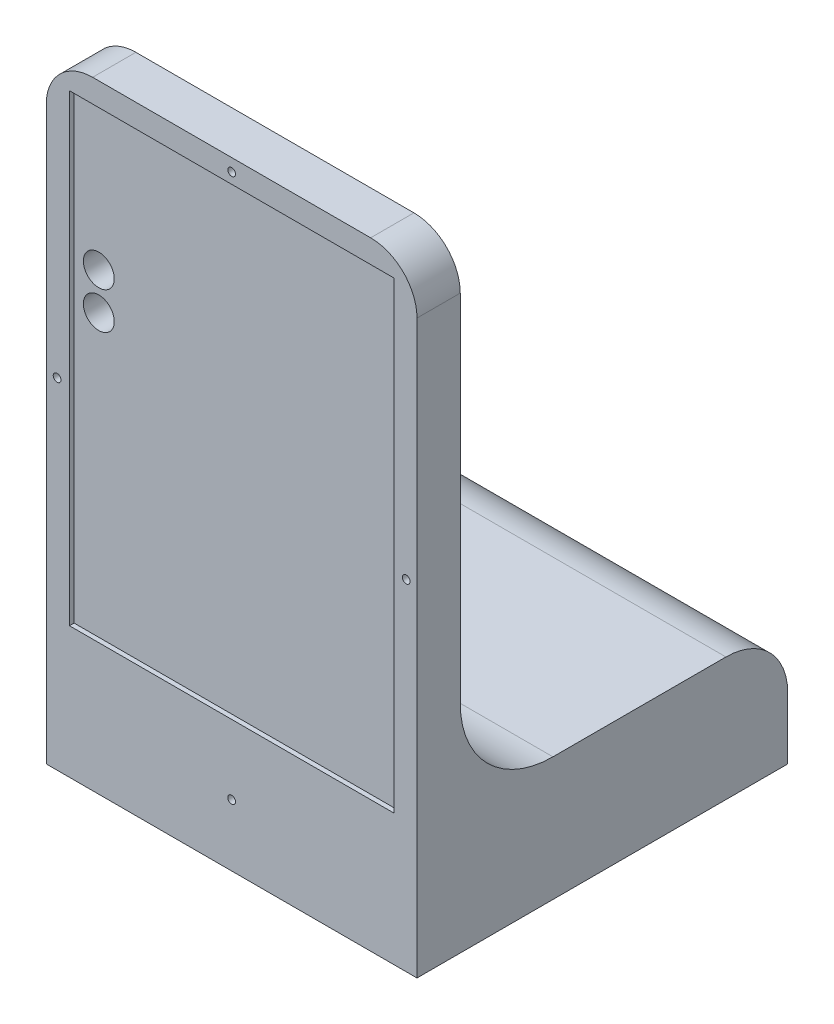
SolidWorks part; units mm, degrees
material "CA"
ref_plane "Plan de face" through (0, 0, 0) normal (0, 0, 1) x (1, 0, 0)
ref_plane "Plan de dessus" through (0, 0, 0) normal (0, 1, 0) x (1, 0, 0)
ref_plane "Plan de droite" through (0, 0, 0) normal (1, 0, 0) x (0, 0, -1)
sketch "Esquisse1" plane through (0, 0, 0) normal (0, 0, 1) x (1, 0, 0)
  line L0 (0, 40) -> (120, 40)
  line L1 (0, 0) -> (120, 0)
  line L2 (0, 0) -> (0, 200)
  line L3 (0, 200) -> (120, 200)
  line L4 (120, 0) -> (120, 200)
  dimension "D1" = 200
  dimension "D2" = 120
  dimension "D3" = 40
extrude "Boss.-Extru.2" add sketch "Esquisse1" along normal mid plane 50 contours L2 L1 L4 L3
sketch "Esquisse3" plane through (0, 0, 25) normal (0, 0, 1) x (1, 0, 0)
  line L0 (120, 0) -> (120, 200) construction
  line L1 (0, 0) -> (120, 0)
  line L2 (0, 0) -> (0, 40)
  line L3 (0, 40) -> (120, 40)
  line L4 (120, 0) -> (120, 40)
  dimension "D1" = 40
extrude "Boss.-Extru.3" add sketch "Esquisse3" along normal blind 70
fillet "Congé1" radius 15 1 edges at (60, 40, 25)
sketch "Esquisse4" plane through (0, 0, -25) normal (0, 0, -1) x (-1, 0, 0)
  line L0 (-120, 0) -> (-120, 200) construction
  line L1 (0, 0) -> (-120, 0)
  line L2 (0, 0) -> (0, 40)
  line L3 (0, 40) -> (-120, 40)
  line L4 (-120, 0) -> (-120, 40)
  dimension "D1" = 40
extrude "Boss.-Extru.4" add sketch "Esquisse4" along normal blind 140
fillet "Congé2" radius 30 1 edges at (60, 40, -25)
sketch "Esquisse5" plane through (0, 0, 95) normal (0, 0, 1) x (1, 0, 0)
  line L0 (0, 0) -> (120, 0) construction
  line L2 (120, 0) -> (120, 40) construction
  line L4 (35, 35) -> (85, 35)
  line L5 (35, 35) -> (35, 5)
  line L6 (35, 5) -> (85, 5)
  line L7 (85, 35) -> (85, 5)
  point P0 (60, 20)
  dimension "D1" = 20
  dimension "D2" = 60
  dimension "D3" = 25
  dimension "D4" = 50
  dimension "D5" = 30
  dimension "D6" = 15
extrude "Boss.-Extru.9" add sketch "Esquisse5" against normal blind 7.5
sketch "Esquisse7" plane through (0, 0, 0) normal (0, -1, 0) x (1, 0, 0)
  line L0 (0, 95) -> (0, -165) construction
  line L1 (10, 85) -> (110, 85)
  line L2 (10, 85) -> (10, 5)
  line L3 (10, 5) -> (110, 5)
  line L4 (110, 85) -> (110, 5)
  line L5 (0, 95) -> (120, 95) construction
  point P4 (60, 45)
  dimension "D1" = 60
  dimension "D2" = 50
  dimension "D3" = 100
  dimension "D4" = 50
  dimension "D5" = 40
  dimension "D6" = 80
extrude "Enlèv. mat.-Extru.1" cut sketch "Esquisse7" against normal blind 35
sketch "Esquisse8" plane through (0, 0, 95) normal (0, 0, 1) x (1, 0, 0)
  line L1 (120, 40) -> (0, 40) construction
  line L2 (0, 40) -> (0, 0) construction
  circle A0 centre (47.5, 20) radius 7.5
  circle A1 centre (72.5, 20) radius 7.5
  dimension "D2" = 15
  dimension "D3" = 15
  dimension "D1" = 25
  dimension "D4" = 20
  dimension "D5" = 47.5
extrude "Enlèv. mat.-Extru.7" cut sketch "Esquisse8" against normal up to next
sketch "Esquisse12" plane through (0, 0, 85) normal (0, 0, -1) x (-1, 0, 0)
  line L0 (-110, 35) -> (-110, 0) construction
  line L1 (-85, 35) -> (-35, 35)
  line L2 (-85, 35) -> (-85, 5)
  line L3 (-85, 5) -> (-35, 5)
  line L4 (-35, 35) -> (-35, 5)
  line L5 (-110, 0) -> (-10, 0) construction
  dimension "D1" = 50
  dimension "D2" = 25
  dimension "D3" = 30
  dimension "D4" = 5
extrude "Enlèv. mat.-Extru.8" cut sketch "Esquisse12" against normal blind 5
sketch "Esquisse13" plane through (120, 0, 0) normal (1, 0, 0) x (0, 0, -1)
  line L0 (-95, 0) -> (-95, 40) construction
  line L1 (-95, 40) -> (-40, 40) construction
  circle A0 centre (-60, 20) radius 12.5
  dimension "D1" = 25
  dimension "D2" = 35
  dimension "D3" = 20
extrude "Enlèv. mat.-Extru.9" cut sketch "Esquisse13" against normal through all and the other way through all
sketch "Esquisse14" plane through (0, 0, 85) normal (0, 0, -1) x (-1, 0, 0)
  line L0 (-120, 0) -> (0, 0) construction
  line L1 (-67.5, 0) -> (-52.5, 0)
  line L2 (-67.5, 0) -> (-67.5, 5)
  line L3 (-67.5, 5) -> (-52.5, 5)
  line L4 (-52.5, 0) -> (-52.5, 5)
  line L5 (-85, 5) -> (-35, 5) construction
  line L6 (-110, 35) -> (-110, 0) construction
  point P8 (-67.5, 2.5)
  dimension "D1" = 0
  dimension "D2" = 42.5
  dimension "D3" = 15
extrude "Enlèv. mat.-Extru.10" cut sketch "Esquisse14" against normal blind 3
sketch "Esquisse19" plane through (0, 0, 0) normal (0, 0, 1) x (1, 0, 0)
sketch "Esquisse22" plane through (0, 0, 0) normal (0, 0, 1) x (1, 0, 0)
  line L0 (-6.4991, 207.2321) -> (136.4343, 207.2321)
  line L1 (-6.4991, 207.2321) -> (-6.4991, -23.3831)
  line L2 (-6.4991, -23.3831) -> (136.4343, -23.3831)
  line L3 (136.4343, 207.2321) -> (136.4343, -23.3831)
extrude "Enlèv. mat.-Extru.12" cut sketch "Esquisse22" along normal blind 141
sketch "Esquisse23" plane through (0, 0, 0) normal (0, 0, 1) x (1, 0, 0)
  line L0 (120, 0) -> (120, 200) construction
  line L1 (7.5, 192.5) -> (112.5, 192.5)
  line L2 (7.5, 192.5) -> (7.5, 42.5)
  line L3 (7.5, 42.5) -> (112.5, 42.5)
  line L4 (112.5, 192.5) -> (112.5, 42.5)
  line L5 (0, 200) -> (120, 200) construction
  dimension "D1" = 105
  dimension "D2" = 150
  dimension "D3" = 7.5
  dimension "D4" = 7.5
extrude "Enlèv. mat.-Extru.13" cut sketch "Esquisse23" against normal blind 12.5
sketch "Esquisse24" plane through (0, 0, 0) normal (0, -1, 0) x (-1, 0, 0)
  line L0 (0, 0) -> (0, 165) construction
  line L1 (-120, 165) -> (0, 165) construction
  circle A0 centre (-76.3227, 105) radius 1.25
  circle A1 centre (-46.3227, 105) radius 1.25
  circle A2 centre (-45, 85) radius 1.25
  circle A3 centre (-75, 85) radius 1.25
  dimension "D1" = 2.5
  dimension "D2" = 2.5
  dimension "D3" = 2.5
  dimension "D4" = 2.5
  dimension "D5" = 45
  dimension "D6" = 30
  dimension "D7" = 30
  dimension "D8" = 20
  dimension "D9" = 34.9627
  dimension "D10" = 37.1633
  dimension "D11" = 20
  dimension "D12" = 60
extrude "Enlèv. mat.-Extru.14" cut sketch "Esquisse24" against normal blind 5
fillet "Congé4" radius 15 3 edges at (60, 40, -165) (0, 200, -12.5) (120, 200, -12.5)
sketch "Esquisse25" plane through (0, 0, 0) normal (1, 0, 0) x (0, 0, -1)
  line L0 (0, 0) -> (165, 0) construction
  line L1 (0, 200) -> (11, 200)
  line L2 (0, 200) -> (0, 0)
  line L3 (0, 0) -> (11, 0)
  line L4 (11, 200) -> (11, 0)
  line L5 (25, 70) -> (25, 185) construction
  dimension "D1" = 14
extrude "Enlèv. mat.-Extru.15" cut sketch "Esquisse25" along normal through all
sketch "Esquisse26" plane through (0, 0, -12.5) normal (0, 0, 1) x (1, 0, 0)
  line L0 (7.5, 192.5) -> (7.5, 42.5) construction
  line L3 (105, 200) -> (15, 200) construction
  circle A0 centre (15.5, 145.5) radius 5
  circle A1 centre (15.5, 133.5) radius 5
  dimension "D3" = 10
  dimension "D4" = 10
  dimension "D6" = 54.5
  dimension "D1" = 8
  dimension "D2" = 8
  dimension "D5" = 12
extrude "Enlèv. mat.-Extru.16" cut sketch "Esquisse26" against normal blind 11 contours A0 | A1
sketch "Esquisse27" plane through (0, 0, 0) normal (1, 0, 0) x (0, 0, -1)
sketch "Esquisse28" plane through (120, 0, 0) normal (1, 0, 0) x (0, 0, -1)
  line L0 (150, 40) -> (55, 40) construction
  line L1 (131, 40) -> (165, 40)
  line L2 (131, 40) -> (131, 0)
  line L3 (131, 0) -> (165, 0)
  line L4 (165, 40) -> (165, 0)
  line L5 (165, 25) -> (165, 0) construction
  dimension "D1" = 34
  dimension "D2" = 40
extrude "Enlèv. mat.-Extru.17" cut sketch "Esquisse28" against normal through all
fillet "Congé5" radius 20 1 edges at (60, 40, -131)
sketch "Esquisse29" plane through (0, 0, -11) normal (0, 0, 1) x (1, 0, 0)
  line L0 (0, 0) -> (0, 185) construction
  line L1 (120, 0) -> (0, 0) construction
  circle A0 centre (60, 20) radius 1.25
  dimension "D1" = 2.5
  dimension "D2" = 60
  dimension "D3" = 20
extrude "Enlèv. mat.-Extru.18" cut sketch "Esquisse29" against normal blind 4
sketch "Esquisse30" plane through (0, 0, -11) normal (0, 0, 1) x (1, 0, 0)
  line L0 (0, 0) -> (0, 185) construction
  line L3 (120, 0) -> (120, 185) construction
  line L4 (105, 200) -> (15, 200) construction
  circle A0 centre (3.5, 110) radius 1.25
  circle A1 centre (116.5, 110) radius 1.25
  circle A2 centre (60, 195.9648) radius 1.25
  dimension "D1" = 2.5
  dimension "D2" = 2.5
  dimension "D3" = 2.5
  dimension "D4" = 60
  dimension "D5" = 3.5
  dimension "D6" = 3.5
  dimension "D7" = 90
  dimension "D8" = 90
extrude "Enlèv. mat.-Extru.19" cut sketch "Esquisse30" against normal through all
